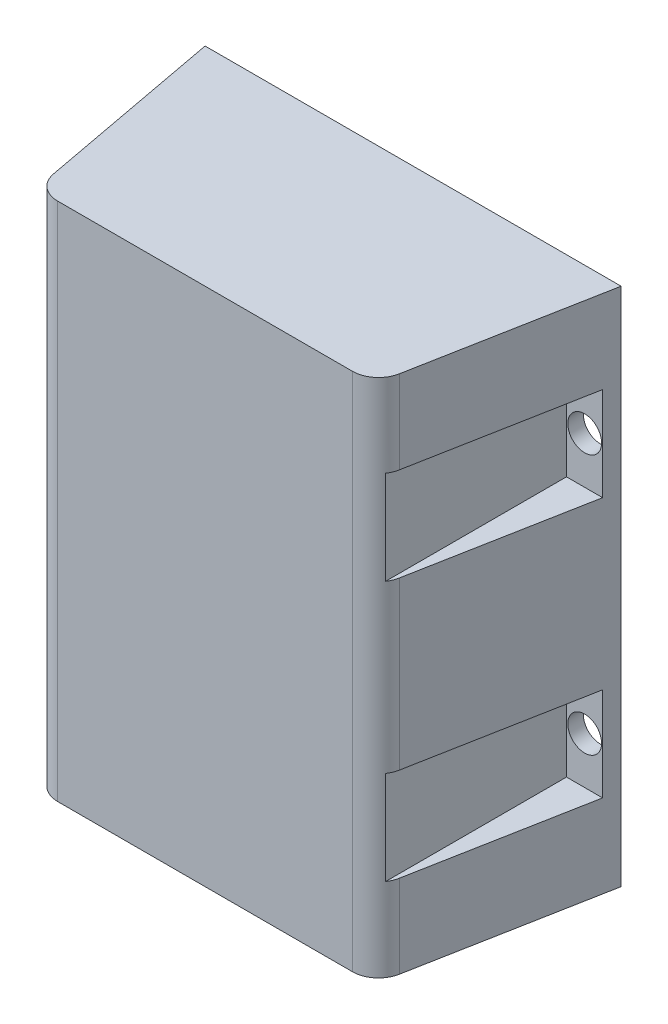
SolidWorks part; units mm, degrees
ref_plane "前视基准面" through (0, 0, 0) normal (0, 0, 1) x (1, 0, 0)
ref_plane "上视基准面" through (0, 0, 0) normal (0, 1, 0) x (1, 0, 0)
ref_plane "右视基准面" through (0, 0, 0) normal (1, 0, 0) x (0, 0, -1)
sketch "草图1" plane through (0, 0, 0) normal (0, 0, 1) x (1, 0, 0)
  line L1 (-40, 50) -> (40, 50)
  line L2 (-40, 50) -> (-40, -50)
  line L3 (-40, -50) -> (40, -50)
  line L4 (40, 50) -> (40, -50)
  line L5 (-40, 50) -> (40, -50) construction
  line L6 (-40, -50) -> (40, 50) construction
  point P0 (0, 0)
extrude "凸台-拉伸1" add sketch "草图1" along normal blind 40
sketch "草图2" plane through (0, -50, 0) normal (0, -1, 0) x (-1, 0, 0)
  line L0 (0, -40) -> (32.5, -40)
  line L1 (40, -40) -> (-40, -40) construction
  line L2 (32.5, -40) -> (40, 0)
  line L3 (40, 0) -> (-40, 0)
  line L4 (0, -40) -> (-32.5, -40)
  line L5 (-32.5, -40) -> (-40, 0)
extrude "切除-拉伸1" cut sketch "草图2" against normal through all both and the other way through all flip side to cut
sketch "草图3" plane through (0, 0, 40) normal (0, 0, 1) x (1, 0, 0)
  line L0 (0, 0) -> (-40, 0) construction
  line L1 (-40, 50) -> (-40, -50) construction
  line L2 (-40, 0) -> (-40, -25) construction
  line L3 (-40, -25) -> (-40, -34)
  line L4 (-40, -34) -> (-32.5, -34)
  line L5 (-32.5, 50) -> (-32.5, -50) construction
  line L6 (-32.5, -34) -> (-32.5, -16)
  line L7 (-32.5, -16) -> (-40, -16)
  line L8 (-40, -16) -> (-40, -25)
  line L9 (-40, 16) -> (-40, 25)
  line L10 (-32.5, 16) -> (-40, 16)
  line L11 (-32.5, 34) -> (-32.5, 16)
  line L12 (-40, 34) -> (-32.5, 34)
  line L13 (-40, 25) -> (-40, 34)
  line L14 (0, 0) -> (0, 20) construction
  line L15 (40, -16) -> (40, -25)
  line L16 (32.5, -16) -> (40, -16)
  line L17 (32.5, -34) -> (32.5, -16)
  line L18 (40, -34) -> (32.5, -34)
  line L19 (40, -25) -> (40, -34)
  line L20 (40, 25) -> (40, 34)
  line L21 (40, 34) -> (32.5, 34)
  line L22 (32.5, 34) -> (32.5, 16)
  line L23 (32.5, 16) -> (40, 16)
  line L24 (40, 16) -> (40, 25)
extrude "切除-拉伸2" cut sketch "草图3" against normal blind 37
sketch "草图4" plane through (0, 0, 3) normal (0, 0, 1) x (1, 0, 0)
  line L0 (-32.5, 25) -> (-36, 25) construction
  line L1 (-32.5, 16) -> (-32.5, 34) construction
  line L2 (0, 0) -> (0, -20) construction
  line L3 (0, 0) -> (20, 0) construction
  circle A0 centre (-36, 25) radius 3.25
  circle A1 centre (36, 25) radius 3.25
  circle A2 centre (36, -25) radius 3.25
  circle A3 centre (-36, -25) radius 3.25
extrude "切除-拉伸3" cut sketch "草图4" against normal blind 37
sketch "草图5" plane through (0, -50, 0) normal (0, -1, 0) x (1, 0, 0)
  line L0 (-28.3504, 40) -> (28.3504, 40)
  line L1 (33.2647, 35.9214) -> (40, 0)
  line L2 (40, 0) -> (-40, 0)
  line L3 (-40, 0) -> (-33.2647, 35.9214)
  arc A0 (33.2647, 35.9214) -> (28.3504, 40) centre (28.3504, 35) ccw
  arc A1 (-28.3504, 40) -> (-33.2647, 35.9214) centre (-28.3504, 35) ccw
  point P10 (32.5, 40)
  point P13 (-32.5, 40)
  dimension "D1" = 5
extrude "切除-拉伸4" cut sketch "草图5" against normal blind 100 flip side to cut
